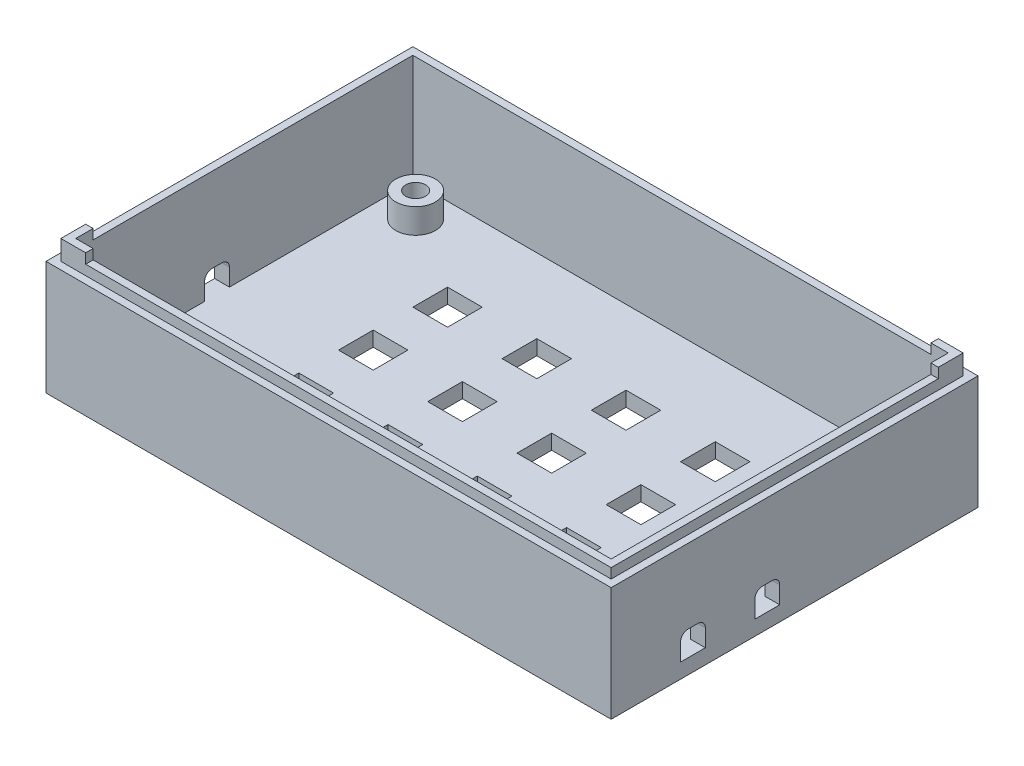
SolidWorks part; units mm, degrees
ref_plane "Plano frontal" through (0, 0, 0) normal (0, 0, 1) x (1, 0, 0)
ref_plane "Plano superior" through (0, 0, 0) normal (0, 1, 0) x (1, 0, 0)
ref_plane "Plano direito" through (0, 0, 0) normal (1, 0, 0) x (0, 0, -1)
sketch "Sketch1" plane through (0, 0, 0) normal (0, 1, 0) x (1, 0, 0)
  line L0 (54, 34) -> (-54, -34) construction
  line L1 (-54, 34) -> (54, 34)
  line L2 (-54, 34) -> (-54, -34)
  line L3 (-54, -34) -> (54, -34)
  line L4 (54, 34) -> (54, -34)
  line L5 (0, 0) -> (0, 34) construction
  line L6 (0, 0) -> (-54, 0) construction
  line L8 (-52.5, -33.0556) -> (52.5, -33.0556) construction
  line L9 (-52.5, -33.0556) -> (-52.5, 33.0556) construction
  line L10 (-52.5, 33.0556) -> (52.5, 33.0556) construction
  line L11 (52.5, -33.0556) -> (52.5, 33.0556) construction
  line L12 (-52.5, -33.0556) -> (52.5, 33.0556) construction
  line L13 (-52.5, 33.0556) -> (52.5, -33.0556) construction
  circle A0 centre (-47.1, 27.6556) radius 2
  circle A1 centre (47.1, 27.6556) radius 2
  circle A2 centre (47.1, -27.6556) radius 2
  circle A3 centre (-47.1, -27.6556) radius 2
  point P7 (-47.1, 29.6556)
  point P8 (-49.1, 27.6556)
  dimension "D3" = 4
  dimension "D1" = 108
  dimension "D2" = 68
  dimension "D4" = 3.4
  dimension "D5" = 3.4
  dimension "D6" = 105
extrude "Boss-Extrude1" add sketch "Sketch1" along normal blind 3
sketch "Sketch2" plane through (0, 3, 0) normal (0, 1, 0) x (1, 0, 0)
  line L0 (-57, 37) -> (-57, -37)
  line L1 (-57, -37) -> (57, -37)
  line L2 (57, -37) -> (57, 37)
  line L3 (57, 37) -> (-57, 37)
  line L4 (-54, 34) -> (-54, -34)
  line L5 (-54, -34) -> (54, -34)
  line L6 (54, -34) -> (54, 34)
  line L7 (54, 34) -> (-54, 34)
  line L8 (-54, 34) -> (-54, -34)
  line L9 (-54, -34) -> (54, -34)
  line L10 (54, -34) -> (54, 34)
  line L11 (54, 34) -> (-54, 34)
  dimension "D1" = 0
  dimension "D2" = 3
extrude "Boss-Extrude2" add sketch "Sketch2" along normal blind 20 and the other way blind 3
sketch "Sketch4" plane through (0, 23, 0) normal (0, 1, 0) x (1, 0, 0)
  line L0 (-55.5, 35.5) -> (-55.5, -35.5)
  line L1 (-54, 34) -> (54, 34)
  line L2 (-54, 34) -> (-54, -34)
  line L3 (-54, -34) -> (54, -34)
  line L4 (54, 34) -> (54, -34)
  line L5 (-55.5, -35.5) -> (55.5, -35.5)
  line L6 (55.5, 35.5) -> (55.5, -35.5)
  line L7 (-55.5, 35.5) -> (55.5, 35.5)
  dimension "D1" = 1.5
extrude "Boss-Extrude3" add sketch "Sketch4" along normal blind 2
sketch "Sketch5" plane through (54, 0, 0) normal (-1, 0, 0) x (0, 0, 1)
  line L0 (34, 3) -> (-34, 3) construction
  line L1 (3, 3) -> (8, 3)
  line L2 (3, 3) -> (3, 6.5)
  line L3 (4.5, 8) -> (6.5, 8)
  line L4 (8, 3) -> (8, 6.5)
  line L5 (34, 3) -> (34, 25) construction
  line L6 (18, 3) -> (23, 3)
  line L7 (18, 3) -> (18, 6.5)
  line L8 (19.5, 8) -> (21.5, 8)
  line L9 (23, 3) -> (23, 6.5)
  arc A0 (23, 6.5) -> (21.5, 8) centre (21.5, 6.5) ccw
  arc A1 (18, 6.5) -> (19.5, 8) centre (19.5, 6.5) cw
  arc A2 (6.5, 8) -> (8, 6.5) centre (6.5, 6.5) cw
  arc A3 (3, 6.5) -> (4.5, 8) centre (4.5, 6.5) cw
  point P14 (23, 8)
  point P17 (18, 8)
  point P20 (8, 8)
  point P23 (3, 8)
  dimension "D7" = 1.5
  dimension "D1" = 5
  dimension "D2" = 5
  dimension "D3" = 5
  dimension "D4" = 5
  dimension "D5" = 11
  dimension "D6" = 10
extrude "Cut-Extrude1" cut sketch "Sketch5" against normal through all
sketch "Sketch6" plane through (0, 3, 0) normal (0, 1, 0) x (1, 0, 0)
  line L0 (0, 0) -> (0, 34) construction
  line L1 (54, 34) -> (-54, 34) construction
  line L2 (-54, 0) -> (0, 0) construction
  line L3 (-54, 34) -> (-54, -34) construction
  circle A0 centre (-47.1, 27.6556) radius 4
  circle A1 centre (-47.1, 27.6556) radius 2
  circle A2 centre (47.1, 27.6556) radius 2
  circle A3 centre (47.1, 27.6556) radius 4
  circle A4 centre (47.1, -27.6556) radius 4
  circle A5 centre (47.1, -27.6556) radius 2
  circle A6 centre (-47.1, -27.6556) radius 2
  circle A7 centre (-47.1, -27.6556) radius 4
  dimension "D1" = 8
extrude "Boss-Extrude4" add sketch "Sketch6" along normal blind 5
sketch "Sketch7" plane through (0, 3, 0) normal (0, 1, 0) x (1, 0, 0)
  line L0 (54, 34) -> (-54, 34) construction
  line L1 (-54, 34) -> (-54, -34) construction
  line L2 (-14, 19) -> (-7, 19)
  line L3 (-32, 19) -> (-25, 19)
  line L4 (-32, 19) -> (-32, 12)
  line L5 (-32, 12) -> (-25, 12)
  line L6 (-25, 19) -> (-25, 12)
  line L7 (-14, 19) -> (-14, 12)
  line L8 (-14, 12) -> (-7, 12)
  line L9 (-7, 19) -> (-7, 12)
  line L10 (4, 19) -> (11, 19)
  line L11 (4, 19) -> (4, 12)
  line L12 (4, 12) -> (11, 12)
  line L13 (11, 19) -> (11, 12)
  line L14 (22, 19) -> (29, 19)
  line L15 (22, 19) -> (22, 12)
  line L16 (22, 12) -> (29, 12)
  line L17 (29, 19) -> (29, 12)
  line L18 (-14, 4) -> (-7, 4)
  line L19 (-14, 4) -> (-14, -3)
  line L20 (-14, -3) -> (-7, -3)
  line L21 (-7, 4) -> (-7, -3)
  line L22 (4, 4) -> (11, 4)
  line L23 (4, 4) -> (4, -3)
  line L24 (4, -3) -> (11, -3)
  line L25 (11, 4) -> (11, -3)
  line L26 (22, 4) -> (29, 4)
  line L27 (22, 4) -> (22, -3)
  line L28 (22, -3) -> (29, -3)
  line L29 (29, 4) -> (29, -3)
  line L30 (-14, -11) -> (-7, -11)
  line L31 (-14, -11) -> (-14, -18)
  line L32 (-14, -18) -> (-7, -18)
  line L33 (-7, -11) -> (-7, -18)
  line L34 (4, -11) -> (11, -11)
  line L35 (4, -11) -> (4, -18)
  line L36 (4, -18) -> (11, -18)
  line L37 (11, -11) -> (11, -18)
  line L38 (22, -11) -> (29, -11)
  line L39 (22, -11) -> (22, -18)
  line L40 (22, -18) -> (29, -18)
  line L41 (29, -11) -> (29, -18)
  line L42 (-32, 4) -> (-25, 4)
  line L43 (-32, 4) -> (-32, -3)
  line L44 (-32, -3) -> (-25, -3)
  line L45 (-25, 4) -> (-25, -3)
  line L46 (-32, -11) -> (-25, -11)
  line L47 (-32, -11) -> (-32, -18)
  line L48 (-32, -18) -> (-25, -18)
  line L49 (-25, -11) -> (-25, -18)
  dimension "D1" = 7
  dimension "D2" = 7
  dimension "D3" = 15
  dimension "D4" = 22
extrude "Cut-Extrude2" cut sketch "Sketch7" against normal through all
mirror "Mirror1" about plane through (0, 0, 0) normal (1, 0, 0) of "Cut-Extrude1"
sketch "Sketch8" plane through (0, 25, 0) normal (0, 1, 0) x (1, 0, 0)
  line L0 (55.5, -35.5) -> (55.5, 35.5) construction
  line L1 (55.5, 35.5) -> (50.5, 35.5)
  line L2 (55.5, 35.5) -> (55.5, 30.5)
  line L3 (55.5, 30.5) -> (54, 30.5)
  line L4 (50.5, 35.5) -> (50.5, 34)
  line L5 (55.5, 35.5) -> (-55.5, 35.5) construction
  line L6 (54, 34) -> (-54, 34) construction
  line L7 (54, 34) -> (50.5, 34)
  line L8 (54, 34) -> (54, 30.5)
  line L11 (54, -34) -> (54, 34) construction
  line L12 (-54, -34) -> (54, -34) construction
  line L13 (-55.5, -35.5) -> (-50.5, -35.5)
  line L14 (-55.5, -35.5) -> (-55.5, -30.5)
  line L15 (-55.5, -30.5) -> (-54, -30.5)
  line L16 (-50.5, -35.5) -> (-50.5, -34)
  line L17 (-54, -34) -> (-50.5, -34)
  line L18 (-54, -34) -> (-54, -30.5)
  line L21 (-54, 34) -> (-54, -34) construction
  dimension "D1" = 5
  dimension "D2" = 5
  dimension "D3" = 5
  dimension "D4" = 5
extrude "Boss-Extrude5" add sketch "Sketch8" along normal blind 2
